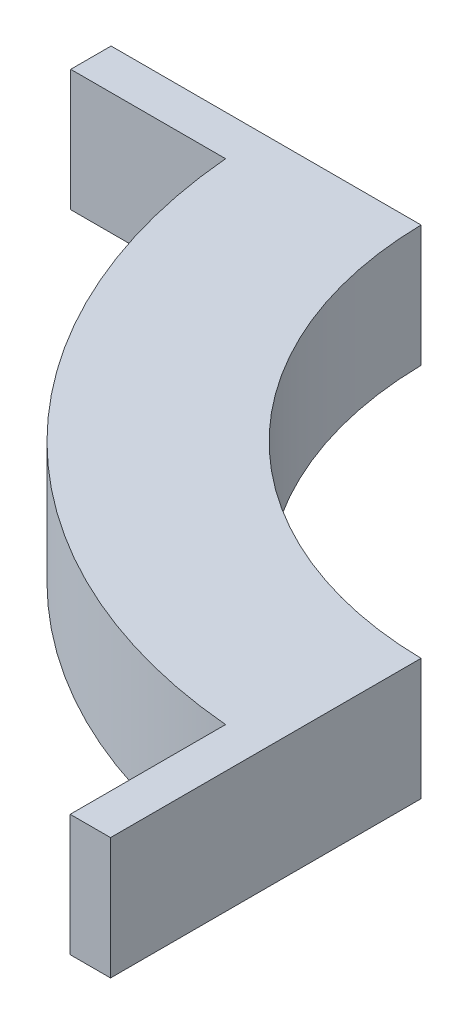
SolidWorks part; units mm, degrees
ref_plane "Front Plane" through (0, 0, 0) normal (0, 0, 1) x (1, 0, 0)
ref_plane "Top Plane" through (0, 0, 0) normal (0, 1, 0) x (1, 0, 0)
ref_plane "Right Plane" through (0, 0, 0) normal (1, 0, 0) x (0, 0, -1)
sketch "Sketch2" plane through (0, 0, 0) normal (0, 1, 0) x (1, 0, 0)
  line L0 (0, 0) -> (-396.7331, 0) construction
  line L3 (-288.8157, -19.3983) -> (-224.1244, -19.3983)
  line L4 (-19.3983, -289.0407) -> (-19.3983, -224.1244)
  line L9 (6.4691, -289.0408) -> (6.4691, -289.0407)
  line L18 (-6.4691, 289.0408) -> (-6.4691, 289.0407)
  line L21 (-224.3494, 19.3983) -> (-224.1244, 19.3983)
  line L33 (-224.3494, 19.3983) -> (-224.1244, 19.3983)
  line L36 (6.4691, 289.0408) -> (6.4691, 289.0407)
  line L39 (0, 0) -> (0, -348.482) construction
  line L40 (-288.8157, -19.3983) -> (-288.8157, -2.54)
  line L41 (-19.3983, -289.0407) -> (-2.54, -289.0407)
  line L42 (-288.8157, -2.54) -> (-159.3249, -2.54)
  line L43 (-2.54, -289.0407) -> (-2.54, -159.3249)
  arc A4 (-224.1244, -19.3983) -> (-19.3983, -224.1244) centre (0, 0) ccw
  arc A7 (-159.3249, -2.54) -> (-2.54, -159.3249) centre (0, 0) ccw
  dimension "D1" = 2.54
  dimension "D3" = 159.3451
  dimension "D2" = 2.54
extrude "Boss-Extrude1" add sketch "Sketch2" along normal blind 50.8
